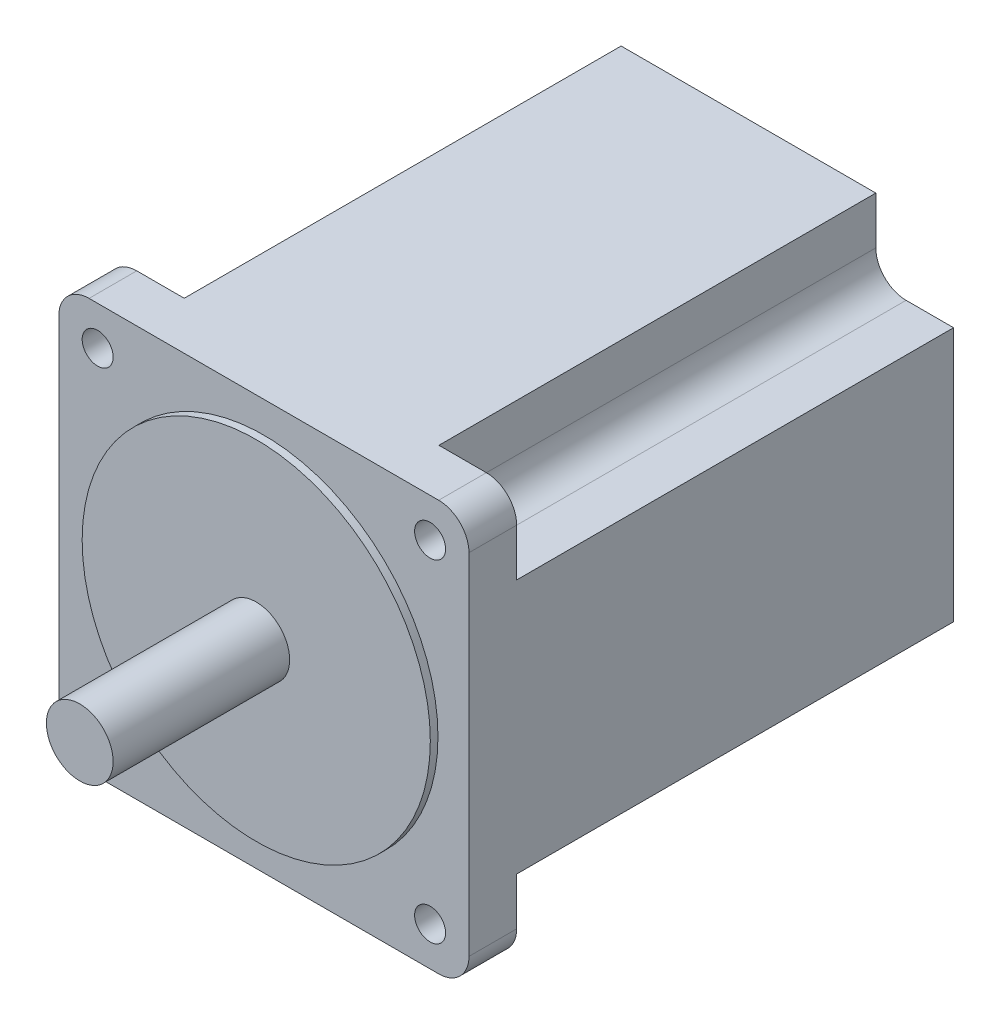
SolidWorks part; units mm, degrees
ref_plane "Front Plane" through (0, 0, 0) normal (0, 0, 1) x (1, 0, 0)
ref_plane "Top Plane" through (0, 0, 0) normal (0, 1, 0) x (1, 0, 0)
ref_plane "Right Plane" through (0, 0, 0) normal (1, 0, 0) x (0, 0, -1)
sketch "Sketch1" plane through (0, 0, 0) normal (0, 0, 1) x (1, 0, 0)
  line L1 (-43, 43) -> (43, 43)
  line L2 (-43, 43) -> (-43, -43)
  line L3 (-43, -43) -> (43, -43)
  line L4 (43, 43) -> (43, -43)
  line L5 (-43, 43) -> (43, -43) construction
  line L6 (-43, -43) -> (43, 43) construction
  point P0 (0, 0)
  dimension "D1" = 86
extrude "Boss-Extrude1" add sketch "Sketch1" against normal blind 101.6
sketch "Sketch2" plane through (0, 0, 0) normal (0, 0, 1) x (1, 0, 0)
  circle A0 centre (0, 0) radius 36.5
  dimension "D1" = 73
extrude "Boss-Extrude2" add sketch "Sketch2" along normal blind 1.6
sketch "Sketch3" plane through (0, 0, 1.6) normal (0, 0, 1) x (1, 0, 0)
  circle A0 centre (0, 0) radius 7
  dimension "D1" = 14
extrude "Boss-Extrude3" add sketch "Sketch3" along normal blind 37
sketch "Sketch5" plane through (0, 0, 0) normal (0, 0, 1) x (1, 0, 0)
  line L1 (-34.85, 34.85) -> (34.85, 34.85) construction
  line L2 (-34.85, 34.85) -> (-34.85, -34.85) construction
  line L3 (-34.85, -34.85) -> (34.85, -34.85) construction
  line L4 (34.85, 34.85) -> (34.85, -34.85) construction
  circle A0 centre (-34.85, 34.85) radius 3.25
  circle A1 centre (34.85, 34.85) radius 3.25
  circle A2 centre (34.85, -34.85) radius 3.25
  circle A3 centre (-34.85, -34.85) radius 3.25
  point P5 (34.85, 0)
  point P7 (0, 34.85)
  dimension "D2" = 6.5
  dimension "D1" = 69.7
extrude "Cut-Extrude1" cut sketch "Sketch5" against normal through all
sketch "Sketch4" plane through (0, 0, -101.6) normal (0, 0, -1) x (-1, 0, 0)
  line L0 (0, 43) -> (0, -43) construction
  line L1 (-43, 43) -> (43, 43) construction
  line L2 (43, -43) -> (-43, -43) construction
  line L3 (-43, 0) -> (43, 0) construction
  line L4 (43, 43) -> (43, -43) construction
  line L5 (-43, -43) -> (-43, 43) construction
  line L6 (-34.85, 43) -> (-34.85, 26.7) construction
  line L7 (-43, 43) -> (-26.7, 43)
  line L8 (-43, 43) -> (-43, 26.7)
  line L9 (-43, 26.7) -> (-26.7, 26.7)
  line L10 (-26.7, 43) -> (-26.7, 26.7)
  line L11 (-43, 34.85) -> (-26.7, 34.85) construction
  line L12 (-43, -34.85) -> (-26.7, -34.85) construction
  line L13 (-34.85, -43) -> (-34.85, -26.7) construction
  line L14 (-26.7, -43) -> (-26.7, -26.7)
  line L15 (-43, -26.7) -> (-26.7, -26.7)
  line L16 (-43, -43) -> (-43, -26.7)
  line L17 (-43, -43) -> (-26.7, -43)
  line L18 (34.85, -43) -> (34.85, -26.7) construction
  line L19 (43, -34.85) -> (26.7, -34.85) construction
  line L20 (43, -43) -> (26.7, -43)
  line L21 (43, -43) -> (43, -26.7)
  line L22 (43, -26.7) -> (26.7, -26.7)
  line L23 (26.7, -43) -> (26.7, -26.7)
  line L24 (43, 34.85) -> (26.7, 34.85) construction
  line L25 (34.85, 43) -> (34.85, 26.7) construction
  line L26 (26.7, 43) -> (26.7, 26.7)
  line L27 (43, 26.7) -> (26.7, 26.7)
  line L28 (43, 43) -> (43, 26.7)
  line L29 (43, 43) -> (26.7, 43)
  circle A1 centre (-34.85, 34.85) radius 3.25 construction
  point P20 (-34.85, 34.85)
extrude "Cut-Extrude2" cut sketch "Sketch4" against normal offset from surface (91.6 mm away) 10 up to face at (-31.6, 34.85, 0)
fillet "Fillet1" radius 6.35 8 edges at (26.7, 26.7, -55.8) (26.7, -26.7, -55.8) (-26.7, -26.7, -55.8) (-43, 43, -5) (-26.7, 26.7, -55.8) (-43, -43, -5) (43, -43, -5) (43, 43, -5)
